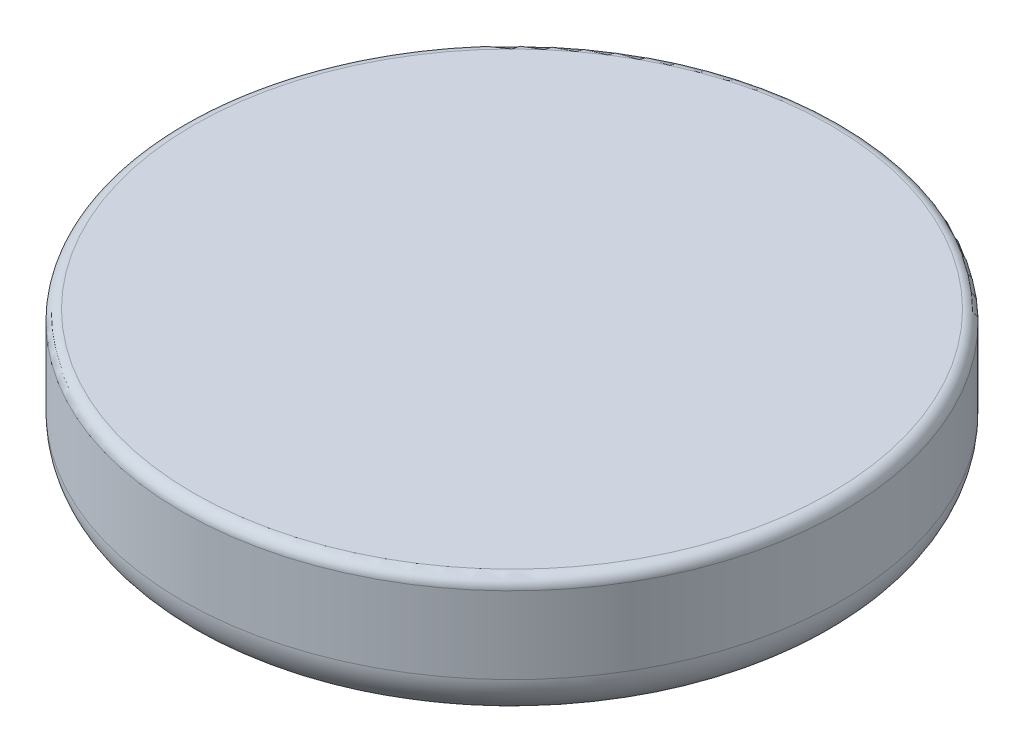
SolidWorks part; units mm, degrees
ref_plane "Front Plane" through (0, 0, 0) normal (0, 0, 1) x (1, 0, 0)
ref_plane "Top Plane" through (0, 0, 0) normal (0, 1, 0) x (1, 0, 0)
ref_plane "Right Plane" through (0, 0, 0) normal (1, 0, 0) x (0, 0, -1)
other "Configuration Table"
sketch "Sketch1" plane through (0, 0, 0) normal (0, 1, 0) x (1, 0, 0)
  circle A0 centre (0, 0) radius 7.5
  dimension "D1" = 15
extrude "Boss-Extrude1" add sketch "Sketch1" along normal blind 3
fillet "Fillet1" radius 1 1 edges at (0, 0, 7.5)
sketch "Sketch2" plane through (0, 0, 0) normal (0, -1, 0) x (1, 0, 0)
  line L1 (0.7, 2.55) -> (-0.7, 2.55)
  line L2 (0.7, 2.55) -> (0.7, -2.55)
  line L3 (0.7, -2.55) -> (-0.7, -2.55)
  line L4 (-0.7, 2.55) -> (-0.7, -2.55)
  line L5 (0.7, 2.55) -> (-0.7, -2.55) construction
  line L6 (0.7, -2.55) -> (-0.7, 2.55) construction
  point P0 (0, 0)
  dimension "D1" = 5.1
  dimension "D2" = 1.4
extrude "Cut-Extrude1" cut sketch "Sketch2" against normal blind 2
fillet "Fillet2" radius 0.25 3 edges at (0, 3, 7.5) (-0.7, 0, 0) (0.7, 0, 0)
